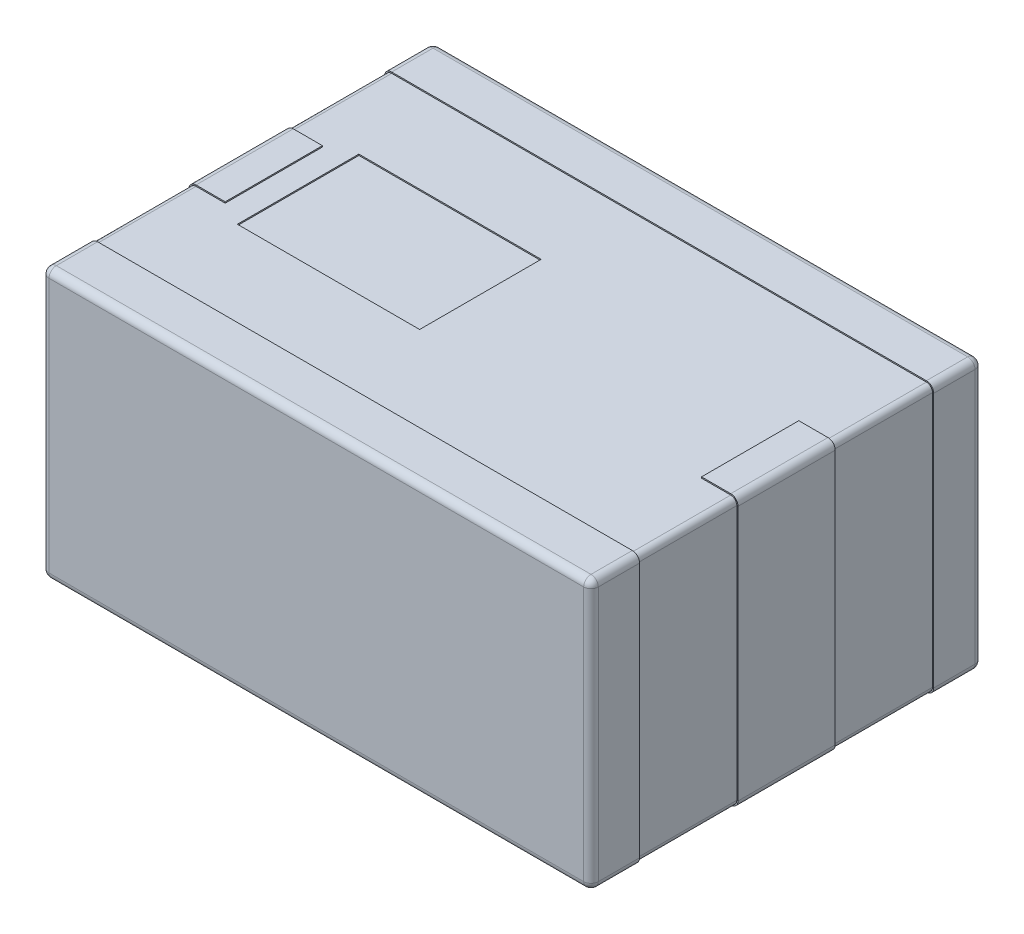
SolidWorks part; units mm, degrees
ref_plane "Front Plane" through (0, 0, 0) normal (0, 0, 1) x (1, 0, 0)
ref_plane "Top Plane" through (0, 0, 0) normal (0, 1, 0) x (1, 0, 0)
ref_plane "Right Plane" through (0, 0, 0) normal (1, 0, 0) x (0, 0, -1)
sketch "Sketch1" plane through (0, 0, 0) normal (0, 1, 0) x (1, 0, 0)
  line L1 (-2.25, 1.6) -> (2.25, 1.6)
  line L2 (-2.25, 1.6) -> (-2.25, -1.6)
  line L3 (-2.25, -1.6) -> (2.25, -1.6)
  line L4 (2.25, 1.6) -> (2.25, -1.6)
  line L5 (-2.25, 1.6) -> (2.25, -1.6) construction
  line L6 (-2.25, -1.6) -> (2.25, 1.6) construction
  point P0 (0, 0)
  dimension "D1" = 4.5
  dimension "D2" = 3.2
extrude "Boss-Extrude1" add sketch "Sketch1" along normal blind 2.2
fillet "Fillet1" radius 0.05 12 edges at (2.25, 1.1, 1.6) (-2.25, 1.1, 1.6) (2.25, 2.2, 0) (0, 2.2, 1.6) (0, 0, 1.6) (2.25, 0, 0) (2.25, 1.1, -1.6) (-2.25, 2.2, 0) (0, 2.2, -1.6) (-2.25, 1.1, -1.6) (-2.25, 0, 0) (0, 0, -1.6)
sketch "Sketch2" plane through (0, 0, 0) normal (0, -1, 0) x (1, 0, 0)
  line L0 (-2.25, 0) -> (2.25, 0) construction
  line L1 (-2.26, 0.4) -> (-1.96, 0.4)
  line L2 (-2.26, 0.4) -> (-2.26, -0.4)
  line L3 (-2.26, -0.4) -> (-1.96, -0.4)
  line L4 (-1.96, 0.4) -> (-1.96, -0.4)
  line L5 (-2.25, -1.6) -> (-2.25, 1.6) construction
  line L6 (2.25, 1.6) -> (2.25, -1.6) construction
  line L7 (0, 0) -> (0, 1.6) construction
  line L8 (-2.25, 1.6) -> (2.25, 1.6) construction
  line L9 (2.26, -0.4) -> (1.96, -0.4)
  line L10 (1.96, 0.4) -> (1.96, -0.4)
  line L11 (2.26, 0.4) -> (1.96, 0.4)
  line L12 (2.26, 0.4) -> (2.26, -0.4)
  line L17 (-2.26, 1.61) -> (2.26, 1.61)
  line L18 (-2.26, 1.61) -> (-2.26, 1.21)
  line L19 (-2.26, 1.21) -> (2.26, 1.21)
  line L20 (2.26, 1.61) -> (2.26, 1.21)
  line L29 (-2.26, -1.61) -> (-2.26, -1.21)
  line L30 (-2.26, -1.21) -> (2.26, -1.21)
  line L31 (2.26, -1.61) -> (2.26, -1.21)
  line L32 (-2.26, -1.61) -> (2.26, -1.61)
  line L37 (-2.2, 1.6) -> (2.2, 1.6) construction
  point P28 (0, 1.61)
  dimension "D1" = 0.8
  dimension "D2" = 0.3
  dimension "D3" = 0.01
  dimension "D4" = 0.01
  dimension "D5" = 0.4
extrude "Boss-Extrude2" add sketch "Sketch2" along normal blind 0.01
sketch "Sketch4" plane through (0, 0, 0) normal (0, -1, 0) x (1, 0, 0)
  line L68 (-1.96, 0.4) -> (-2.26, 0.4)
  line L69 (-1.96, -0.4) -> (-1.96, 0.4)
  line L70 (-2.26, -0.4) -> (-1.96, -0.4)
  line L71 (-2.26, 0.4) -> (-2.26, -0.4)
  line L72 (-1.96, 0.4) -> (-2.26, 0.4)
  line L73 (-1.96, -0.4) -> (-1.96, 0.4)
  line L74 (-2.26, -0.4) -> (-1.96, -0.4)
  line L75 (-2.26, 0.4) -> (-2.26, -0.4)
  line L76 (2.26, 1.61) -> (-2.26, 1.61)
  line L77 (2.26, 1.21) -> (2.26, 1.61)
  line L78 (-2.26, 1.21) -> (2.26, 1.21)
  line L79 (-2.26, 1.61) -> (-2.26, 1.21)
  line L80 (2.26, 1.61) -> (-2.26, 1.61)
  line L81 (2.26, 1.21) -> (2.26, 1.61)
  line L82 (-2.26, 1.21) -> (2.26, 1.21)
  line L83 (-2.26, 1.61) -> (-2.26, 1.21)
  line L84 (1.96, 0.4) -> (1.96, -0.4)
  line L85 (2.26, 0.4) -> (1.96, 0.4)
  line L86 (2.26, -0.4) -> (2.26, 0.4)
  line L87 (1.96, -0.4) -> (2.26, -0.4)
  line L88 (1.96, 0.4) -> (1.96, -0.4)
  line L89 (2.26, 0.4) -> (1.96, 0.4)
  line L90 (2.26, -0.4) -> (2.26, 0.4)
  line L91 (1.96, -0.4) -> (2.26, -0.4)
  line L92 (-2.26, -1.21) -> (-2.26, -1.61)
  line L93 (2.26, -1.21) -> (-2.26, -1.21)
  line L94 (2.26, -1.61) -> (2.26, -1.21)
  line L95 (-2.26, -1.61) -> (2.26, -1.61)
  line L96 (-2.26, -1.21) -> (-2.26, -1.61)
  line L97 (2.26, -1.21) -> (-2.26, -1.21)
  line L98 (2.26, -1.61) -> (2.26, -1.21)
  line L99 (-2.26, -1.61) -> (2.26, -1.61)
  dimension "D1" = 0
  dimension "D2" = 0
  dimension "D3" = 0
  dimension "D4" = 0
extrude "Boss-Extrude3" add sketch "Sketch4" against normal blind 2.21
sketch "Sketch3" plane through (0, 2.2, 0) normal (0, 1, 0) x (1, 0, 0)
  line L0 (-2.26, 0) -> (1, 0) construction
  line L3 (-2.26, -0.4) -> (-2.26, 0.4) construction
  line L4 (-1.76, 0.5) -> (-0.26, 0.5)
  line L5 (-1.76, 0.5) -> (-1.76, -0.5)
  line L6 (-1.76, -0.5) -> (-0.26, -0.5)
  line L7 (-0.26, 0.5) -> (-0.26, -0.5)
  dimension "D1" = 0.5
  dimension "D2" = 1.5
  dimension "D3" = 1
extrude "Cut-Extrude1" cut sketch "Sketch3" against normal blind 0.01
fillet "Fillet2" radius 0.06 20 edges at (-2.26, -0.01, 0) (0, -0.01, -1.61) (2.26, -0.01, 0) (0, -0.01, 1.61) (-2.26, 2.21, 0) (2.26, 2.21, 0) (2.26, 1.1, -1.61) (2.26, 2.21, -1.41) (0, 2.21, -1.61) (-2.26, 2.21, -1.41) (-2.26, 1.1, -1.61) (2.26, -0.01, -1.41) (-2.26, -0.01, -1.41) (2.26, -0.01, 1.41) (-2.26, -0.01, 1.41) (-2.26, 1.1, 1.61) (2.26, 1.1, 1.61) (2.26, 2.21, 1.41) (0, 2.21, 1.61) (-2.26, 2.21, 1.41)
